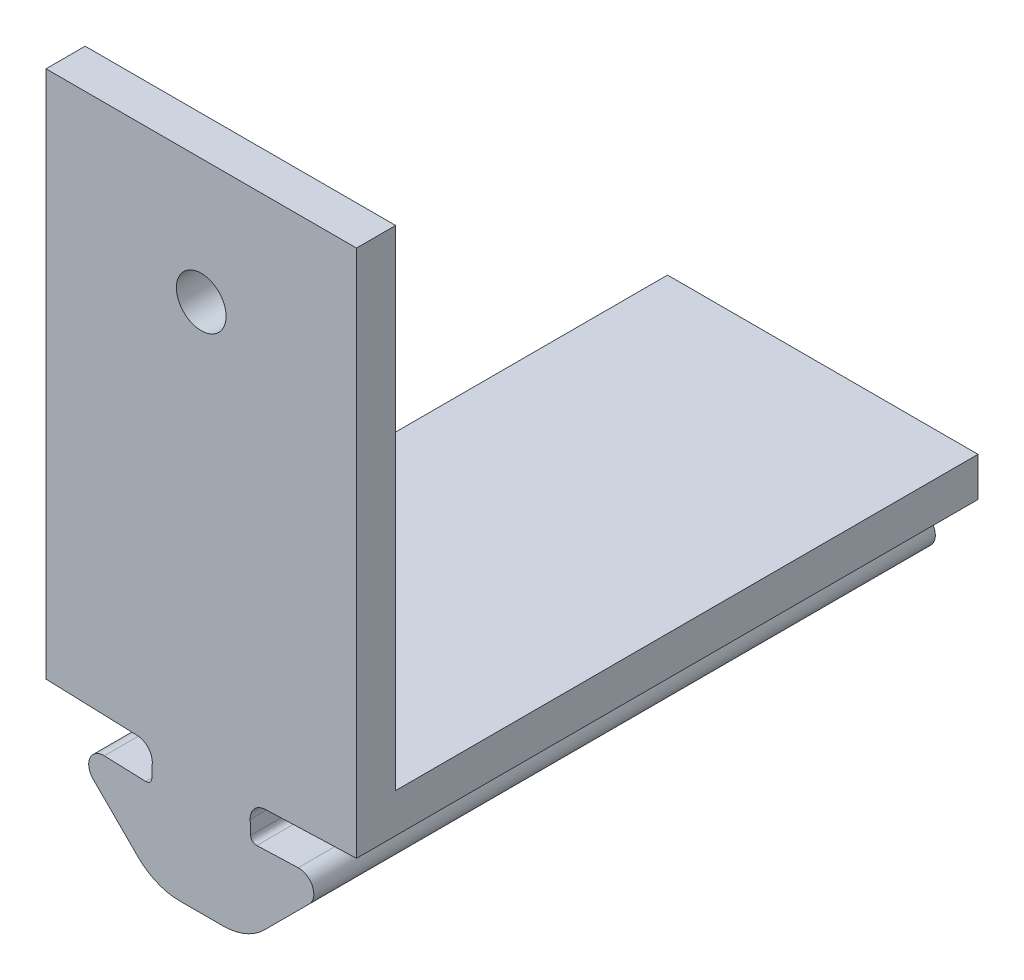
SolidWorks part; units mm, degrees
ref_plane "Front Plane" through (0, 0, 0) normal (0, 0, 1) x (1, 0, 0)
ref_plane "Top Plane" through (0, 0, 0) normal (0, 1, 0) x (1, 0, 0)
ref_plane "Right Plane" through (0, 0, 0) normal (1, 0, 0) x (0, 0, -1)
sketch "Sketch2" plane through (0, 0, 0) normal (0, 0, 1) x (1, 0, 0)
  line L1 (-50.3756, 45.6099) -> (-50.3512, 46.3094)
  line L2 (-50.6859, 45.3205) -> (-52.8037, 45.3945)
  line L6 (-55.7809, 47.2995) -> (-51.1228, 47.1369)
  line L7 (-51.0743, 41.7794) -> (-53.3751, 44.0803)
  line L8 (-47.8507, 40.9008) -> (-48.9529, 40.9008)
  line L9 (-47.8507, 40.9008) -> (-47.8507, 47.2995)
  line L10 (-47.8507, 47.2995) -> (-55.7809, 47.2995)
  arc A0 (-50.6859, 45.3205) -> (-50.3756, 45.6099) centre (-50.6754, 45.6203) ccw
  arc A7 (-50.3512, 46.3094) -> (-51.1228, 47.1369) centre (-51.1507, 46.3374) ccw
  arc A8 (-52.8037, 45.3945) -> (-53.3751, 44.0803) centre (-52.8306, 44.6248) ccw
  arc A9 (-51.0743, 41.7794) -> (-48.9529, 40.9008) centre (-48.9529, 43.9008) ccw
extrude "Boss-Extrude1" add sketch "Sketch2" along normal blind 31.75
ref_plane "Plane2" through (0, 0, 0) normal (0.7071, -0.7071, 0) x (-0.7071, -0.7071, 0)
ref_plane "Plane3" through (-42.746, 42.746, 0) normal (0.7071, -0.7071, 0) x (-0.7071, -0.7071, 0)
mirror "Mirror2" about plane through (-47.8507, 40.9008, 31.75) normal (-1, 0, 0) of "Boss-Extrude1"
ref_plane "Plane7" through (0, 47.2995, 0) normal (0, 1, 0) x (1, 0, 0)
sketch "Sketch19" plane through (0, 47.2995, 0) normal (0, 1, 0) x (1, 0, 0)
  line L0 (-55.7809, -31.75) -> (-55.7809, 0) construction
  line L1 (-55.7809, 0) -> (-39.9205, 0)
  line L2 (-55.7809, 0) -> (-55.7809, -31.75)
  line L3 (-55.7809, -31.75) -> (-39.9205, -31.75)
  line L4 (-39.9205, 0) -> (-39.9205, -31.75)
  line L5 (-39.9205, -31.75) -> (-39.9205, 0) construction
  line L6 (-39.9205, 0) -> (-55.7809, 0) construction
  dimension "D1" = 0
  dimension "D2" = 31.75
extrude "Boss-Extrude7" add sketch "Sketch19" along normal blind 2
sketch "Sketch23" plane through (0, 49.2995, 0) normal (0, 1, 0) x (1, 0, 0)
  line L0 (-55.7809, 0) -> (-55.7809, -31.75) construction
  line L1 (-55.7809, -29.75) -> (-39.9205, -29.75)
  line L2 (-55.7809, -29.75) -> (-55.7809, -31.75)
  line L3 (-55.7809, -31.75) -> (-39.9205, -31.75)
  line L4 (-39.9205, -29.75) -> (-39.9205, -31.75)
  line L5 (-39.9205, -31.75) -> (-39.9205, 0) construction
  line L8 (-55.7809, -31.75) -> (-39.9205, -31.75) construction
  dimension "D1" = 0
  dimension "D2" = 0
  dimension "D3" = 0
  dimension "D4" = 2
extrude "Boss-Extrude8" add sketch "Sketch23" along normal blind 25
ref_plane "Plane8" through (-39.9205, 49.2995, 29.75) normal (0, -1, 0) x (-1, 0, 0)
sketch "Sketch24" plane through (0, 0, 29.75) normal (0, 0, -1) x (-1, 0, 0)
  line L0 (39.9205, 74.2995) -> (55.7809, 74.2995) construction
  line L5 (47.8507, 74.2995) -> (47.8507, 61.5995) construction
  circle A1 centre (47.8507, 67.9495) radius 1.27
  dimension "D1" = 6.35
  dimension "D4" = 2.54
extrude "Cut-Extrude1" cut sketch "Sketch24" against normal blind 2.54
